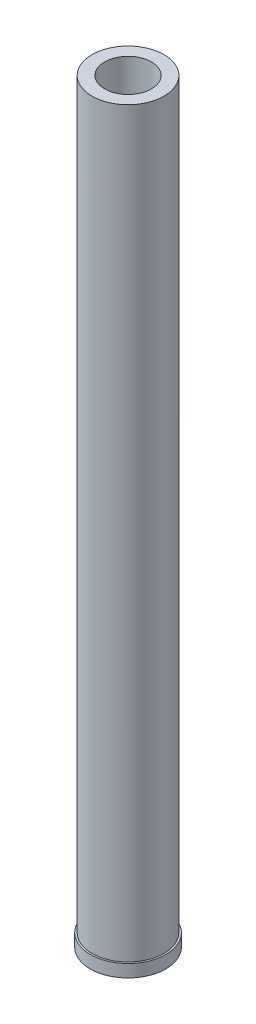
SolidWorks part; units mm, degrees
ref_plane "Front Plane" through (0, 0, 0) normal (0, 0, 1) x (1, 0, 0)
ref_plane "Top Plane" through (0, 0, 0) normal (0, 1, 0) x (1, 0, 0)
ref_plane "Right Plane" through (0, 0, 0) normal (1, 0, 0) x (0, 0, -1)
sketch "Sketch1" plane through (0, 0, 0) normal (0, 1, 0) x (1, 0, 0)
  circle A0 centre (0, 0) radius 14.3
  circle A1 centre (0, 0) radius 9.3
  dimension "D1" = 28.6
  dimension "D2" = 5
extrude "Boss-Extrude1" add sketch "Sketch1" along normal blind 300
sketch "Sketch2" plane through (0, 0, 0) normal (0, 0, 1) x (1, 0, 0)
  line L0 (0, 0) -> (0, 50000) construction
  line L1 (-15, 5) -> (15, 5)
  line L2 (-15, 5) -> (-15, 0)
  line L3 (-15, 0) -> (15, 0)
  line L4 (15, 5) -> (15, 0)
  line L5 (0, 0) -> (0, 5) construction
  line L6 (-15, 2.5) -> (15, 2.5) construction
  line L8 (-14.3, 5) -> (-14.3, 0)
  point P180 (0, 2.5)
  dimension "D1" = 30
  dimension "D2" = 5
  dimension "D3" = 0
  dimension "D4" = 14.3
revolve "Revolve1" add sketch "Sketch2" angle 360 about L0
